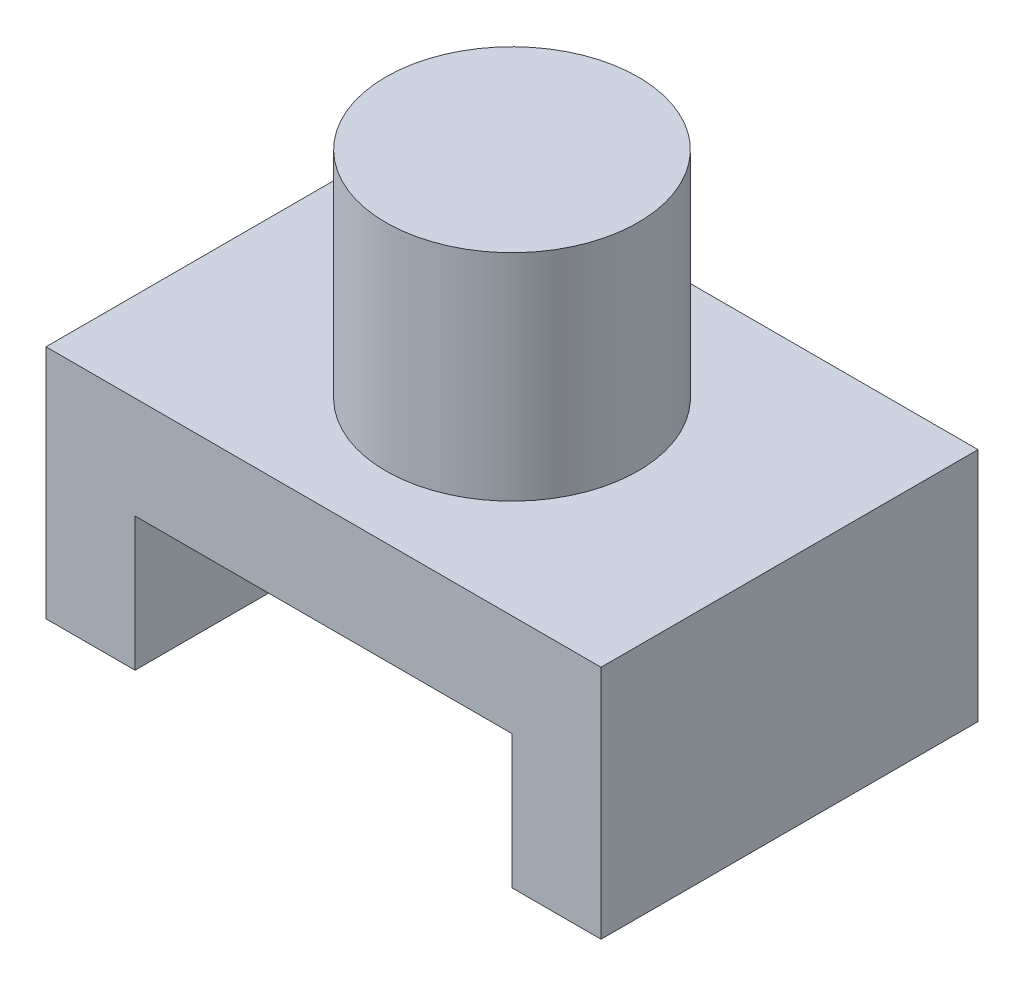
SolidWorks part; units mm, degrees
ref_plane "Front Plane" through (0, 0, 0) normal (0, 0, 1) x (1, 0, 0)
ref_plane "Top Plane" through (0, 0, 0) normal (0, 1, 0) x (1, 0, 0)
ref_plane "Right Plane" through (0, 0, 0) normal (1, 0, 0) x (0, 0, -1)
sketch "Sketch1" plane through (0, 0, 0) normal (0, 0, 1) x (1, 0, 0)
  line L0 (-10.1895, 0) -> (-10.1895, 9)
  line L1 (-10.1895, 9) -> (15.2105, 9)
  line L2 (15.2105, 9) -> (15.2105, 0)
  line L3 (15.2105, 0) -> (21.2105, 0)
  line L4 (21.2105, 0) -> (21.2105, 15.875)
  line L5 (21.2105, 15.875) -> (-16.1895, 15.875)
  line L6 (-16.1895, 15.875) -> (-16.1895, 0)
  line L7 (-16.1895, 0) -> (-10.1895, 0)
  dimension "D1" = 25.4
  dimension "D2" = 9
  dimension "D3" = 15.875
  dimension "D4" = 6
  dimension "D5" = 6
extrude "Boss-Extrude1" add sketch "Sketch1" along normal blind 25.4
sketch "Sketch2" plane through (0, 15.875, 0) normal (0, 1, 0) x (1, 0, 0)
  line L0 (2.5105, -25.4) -> (2.5105, 0) construction
  line L1 (21.2105, -25.4) -> (-16.1895, -25.4) construction
  line L2 (21.2105, 0) -> (-16.1895, 0) construction
  circle A0 centre (2.5105, -12.7) radius 8.5
  dimension "D1" = 17
extrude "Boss-Extrude2" add sketch "Sketch2" along normal blind 14.5
